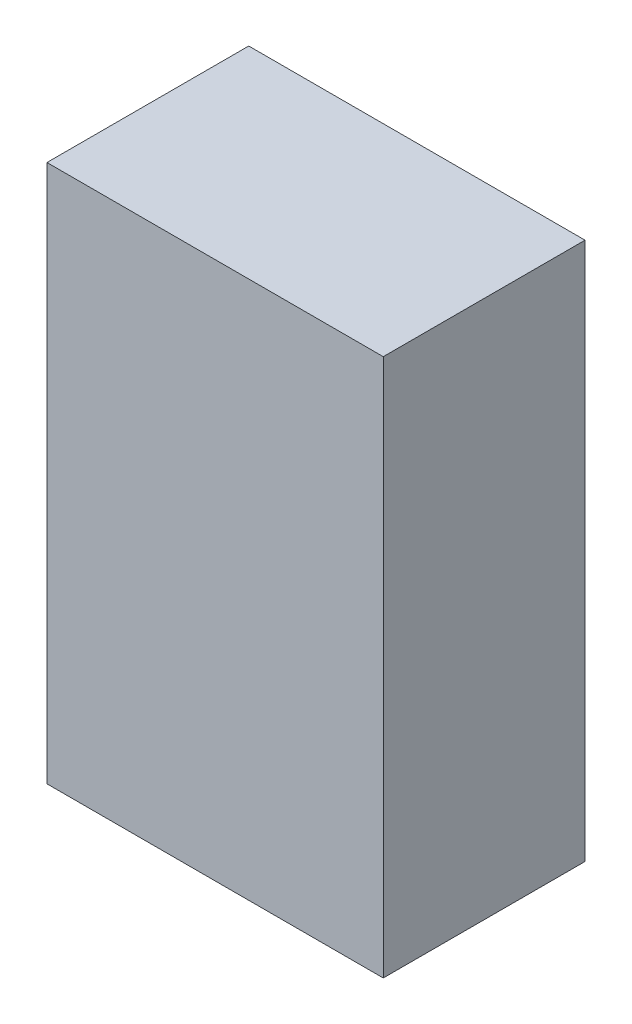
SolidWorks part; units mm, degrees
ref_plane "Front Plane" through (0, 0, 0) normal (0, 0, 1) x (1, 0, 0)
ref_plane "Top Plane" through (0, 0, 0) normal (0, 1, 0) x (1, 0, 0)
ref_plane "Right Plane" through (0, 0, 0) normal (1, 0, 0) x (0, 0, -1)
sketch "Sketch1" plane through (0, 0, 0) normal (0, 0, 1) x (1, 0, 0)
  line L1 (-2.5, 4) -> (2.5, 4)
  line L2 (-2.5, 4) -> (-2.5, -4)
  line L3 (-2.5, -4) -> (2.5, -4)
  line L4 (2.5, 4) -> (2.5, -4)
  line L5 (-2.5, 4) -> (2.5, -4) construction
  line L6 (-2.5, -4) -> (2.5, 4) construction
  point P0 (0, 0)
  dimension "D1" = 5
  dimension "D2" = 8
extrude "Boss-Extrude1" add sketch "Sketch1" along normal mid plane 3
